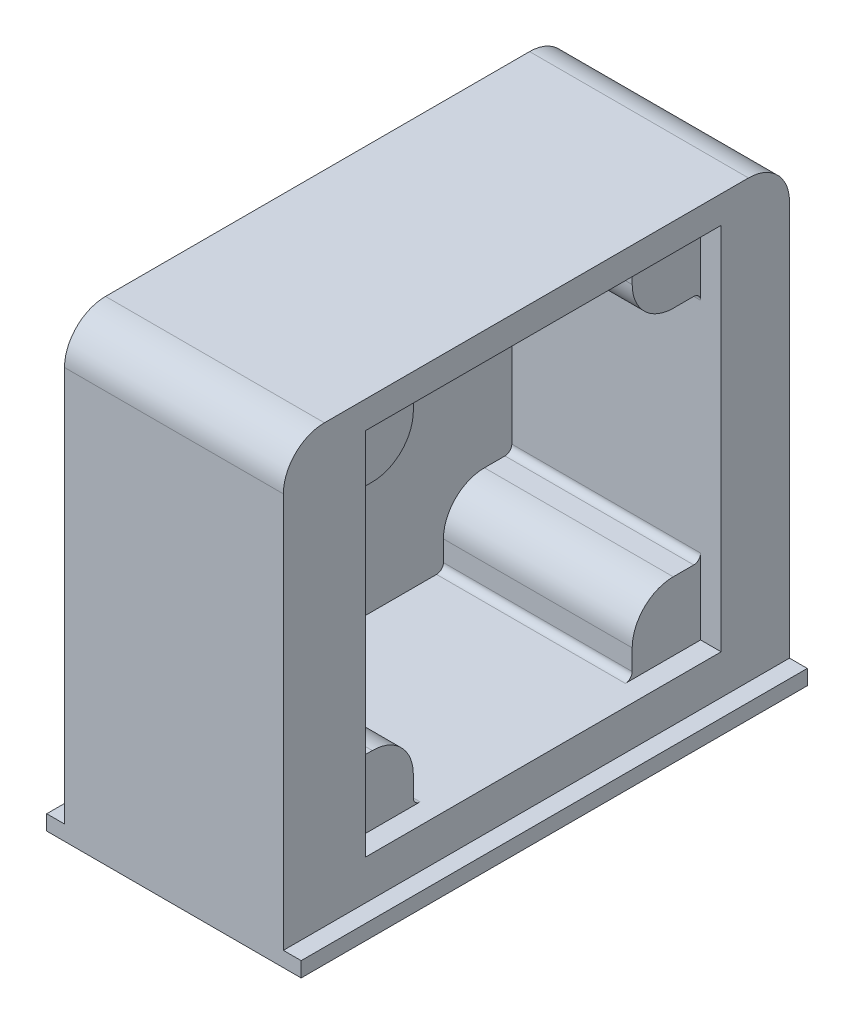
SolidWorks part; units mm, degrees
ref_plane "Front Plane" through (0, 0, 0) normal (0, 0, 1) x (1, 0, 0)
ref_plane "Top Plane" through (0, 0, 0) normal (0, 1, 0) x (1, 0, 0)
ref_plane "Right Plane" through (0, 0, 0) normal (1, 0, 0) x (0, 0, -1)
sketch "Sketch1" plane through (0, 0, 0) normal (0, 0, 1) x (1, 0, 0)
  line L0 (-8, -16.5) -> (-9.3, -16.5)
  line L1 (-8, -16.5) -> (8, -16.5)
  line L2 (-8, -15.4) -> (-8, 16.5)
  line L3 (-8, 16.5) -> (8, 16.5)
  line L4 (8, -15.4) -> (8, 16.5)
  line L5 (-8, -16.5) -> (8, 16.5) construction
  line L6 (-8, 16.5) -> (8, -16.5) construction
  line L7 (-9.3, -16.5) -> (-9.3, -15.4)
  line L8 (-9.3, -15.4) -> (-8, -15.4)
  line L9 (-8, -15.4) -> (9.3, -15.4) construction
  line L10 (8, -15.4) -> (9.3, -15.4)
  line L11 (9.3, -15.4) -> (9.3, -16.5)
  line L12 (9.3, -16.5) -> (8, -16.5)
  line L13 (-8, -15.4) -> (-8, -16.5) construction
  line L14 (8, -15.4) -> (8, -16.5) construction
  point P0 (0, 0)
  dimension "D1" = 16
  dimension "D2" = 33
  dimension "D3" = 1.1
  dimension "D4" = 1.3
extrude "Boss-Extrude1" add sketch "Sketch1" along normal blind 37
sketch "Sketch2" plane through (8, 0, 0) normal (-1, 0, 0) x (0, 0, 1)
  line L0 (0, 16.5) -> (0, -15.4) construction
  line L1 (5, -12.5) -> (31, -12.5)
  line L2 (5, -12.5) -> (5, 14.5)
  line L3 (5, 14.5) -> (31, 14.5)
  line L4 (31, -12.5) -> (31, 14.5)
  line L5 (5, -12.5) -> (31, 14.5) construction
  line L6 (5, 14.5) -> (31, -12.5) construction
  line L7 (37, 16.5) -> (0, 16.5) construction
  point P0 (18, 1)
  dimension "D1" = 5
  dimension "D2" = 2
  dimension "D3" = 27
  dimension "D4" = 26
extrude "Cut-Extrude2" cut sketch "Sketch2" along normal blind 15.3
sketch "Sketch3" plane through (-7.3, 0, 0) normal (1, 0, 0) x (0, 0, -1)
  line L0 (-31, 9.5) -> (-5, 9.5) construction
  line L1 (-31, -12.5) -> (-31, 14.5) construction
  line L2 (-5, 14.5) -> (-5, -12.5) construction
  line L3 (-31, -7.5) -> (-5, -7.5) construction
  line L4 (-26, -12.5) -> (-26, 14.5) construction
  line L5 (-5, -12.5) -> (-31, -12.5) construction
  line L6 (-31, 14.5) -> (-5, 14.5) construction
  line L7 (-10, -12.5) -> (-10, 14.5) construction
  line L8 (-31, -12.5) -> (-31, 14.5) construction
  line L9 (-5, 14.5) -> (-5, -12.5) construction
  line L10 (-31, 14.5) -> (-5, 14.5) construction
  line L12 (-31, 14.5) -> (-26, 14.5)
  line L13 (-31, 14.5) -> (-31, 9.5)
  line L14 (-31, 9.5) -> (-26, 9.5)
  line L15 (-26, 14.5) -> (-26, 9.5)
  line L16 (-10, 9.5) -> (-5, 9.5)
  line L17 (-10, 9.5) -> (-10, 14.5)
  line L18 (-10, 14.5) -> (-5, 14.5)
  line L19 (-5, 9.5) -> (-5, 14.5)
  line L20 (-5, -12.5) -> (-10, -12.5)
  line L21 (-5, -12.5) -> (-5, -7.5)
  line L22 (-5, -7.5) -> (-10, -7.5)
  line L23 (-10, -12.5) -> (-10, -7.5)
  line L24 (-31, -12.5) -> (-26, -12.5)
  line L25 (-31, -12.5) -> (-31, -7.5)
  line L26 (-31, -7.5) -> (-26, -7.5)
  line L27 (-26, -12.5) -> (-26, -7.5)
  dimension "D1" = 5
  dimension "D3" = 5
  dimension "D4" = 5
extrude "Boss-Extrude2" add sketch "Sketch3" along normal blind 13.8
fillet "Fillet1" radius 0.5 6 edges at (-0.4, -7.5, 31) (-0.4, -12.5, 26) (-0.4, -12.5, 10) (-0.4, -7.5, 5) (-0.4, 9.5, 5) (-0.4, 9.5, 31)
fillet "Fillet2" radius 3 4 edges at (-0.4, -7.5, 26) (-0.4, -7.5, 10) (-0.4, 9.5, 10) (-0.4, 9.5, 26)
sketch "Sketch4" plane through (0, 14.5, 0) normal (0, -1, 0) x (1, 0, 0)
  line L0 (-7.3, 26) -> (-7.3, 10) construction
  line L1 (-7.3, 10) -> (6.5, 10)
  line L2 (-7.3, 10) -> (-7.3, 26)
  line L3 (-7.3, 26) -> (6.5, 26)
  line L4 (8, 10) -> (8, 26) construction
  line L5 (8, 31) -> (8, 5) construction
  line L6 (8, 31) -> (8, 26) construction
  line L7 (8, 10) -> (8, 5) construction
  line L8 (6.5, 26) -> (6.5, 10)
  line L9 (6.5, 26) -> (8, 26) construction
  line L10 (8, 10) -> (6.5, 10) construction
  dimension "D1" = 5
  dimension "D2" = 3
extrude "Cut-Extrude3" cut sketch "Sketch4" against normal blind 1
fillet "Fillet3" radius 1 2 edges at (-0.4, 15.5, 10) (-0.4, 15.5, 26)
fillet "Fillet4" radius 3 2 edges at (0, 16.5, 0) (0, 16.5, 37)
